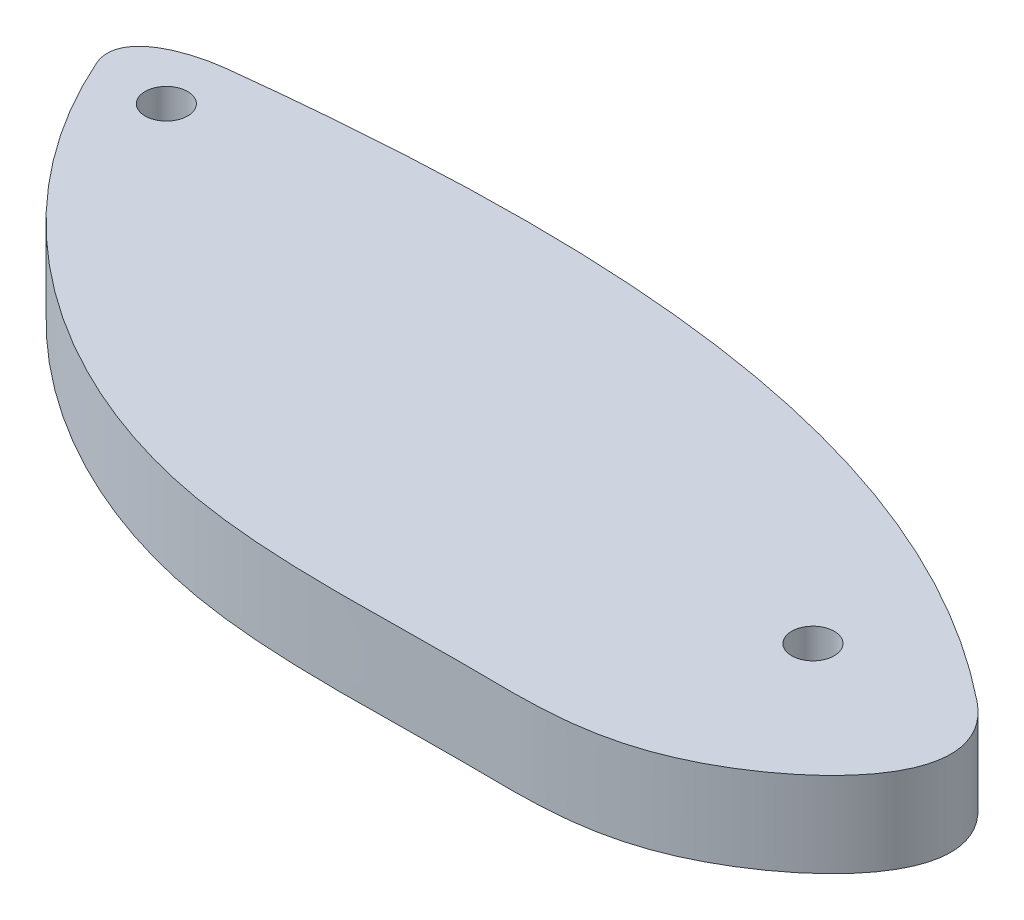
SolidWorks part; units mm, degrees
ref_plane "Front Plane" through (0, 0, 0) normal (0, 0, 1) x (1, 0, 0)
ref_plane "Top Plane" through (0, 0, 0) normal (0, 1, 0) x (1, 0, 0)
ref_plane "Right Plane" through (0, 0, 0) normal (1, 0, 0) x (0, 0, -1)
sketch "Sketch1" plane through (0, 0, 0) normal (0, 1, 0) x (1, 0, 0)
  line L0 (53.2769, 94.4) -> (266.3844, 94.4) construction
  line L1 (0, 0) -> (152.4, 0) construction
  line L2 (152.4, 0) -> (152.4, 90.0113) construction
  line L3 (152.4, 90.0113) -> (0, 90.0113) construction
  line L4 (0, 90.0113) -> (0, 0) construction
  circle A0 centre (52.0232, 14.4432) radius 0.7937
  circle A1 centre (81.5332, 9.063) radius 0.7937
  spline S0 degree 3 poles (49.4122, 14.4432) (50.7616, 11.3929) (55.173, 5.9152) (64.9786, 1.399) (75.1472, 2.0897) (83.1058, 1.5539) (89.4164, 7.8886) (86.4631, 10.2566) knots 0 0 0 0 0.211072 0.438109 0.667267 0.840751 1 1 1 1
  spline S1 degree 3 poles (86.4631, 10.2566) (83.213, 12.8624) (73.8988, 17.3296) (61.5773, 17.6559) (53.6454, 16.8884) (52.0232, 16.7038) knots 0 0 0 0 0.334482 0.861936 1 1 1 1
  spline S2 degree 3 poles (49.4122, 14.4432) (48.7995, 15.828) (50.6006, 16.5419) (52.0232, 16.7038) knots 0 0 0 0 1 1 1 1
  dimension "D3" = 1.5875
  dimension "D4" = 1.5875
  dimension "D1" = 90.0113
  dimension "D2" = 152.4
extrude "Boss-Extrude1" add sketch "Sketch1" along normal blind 3.175
